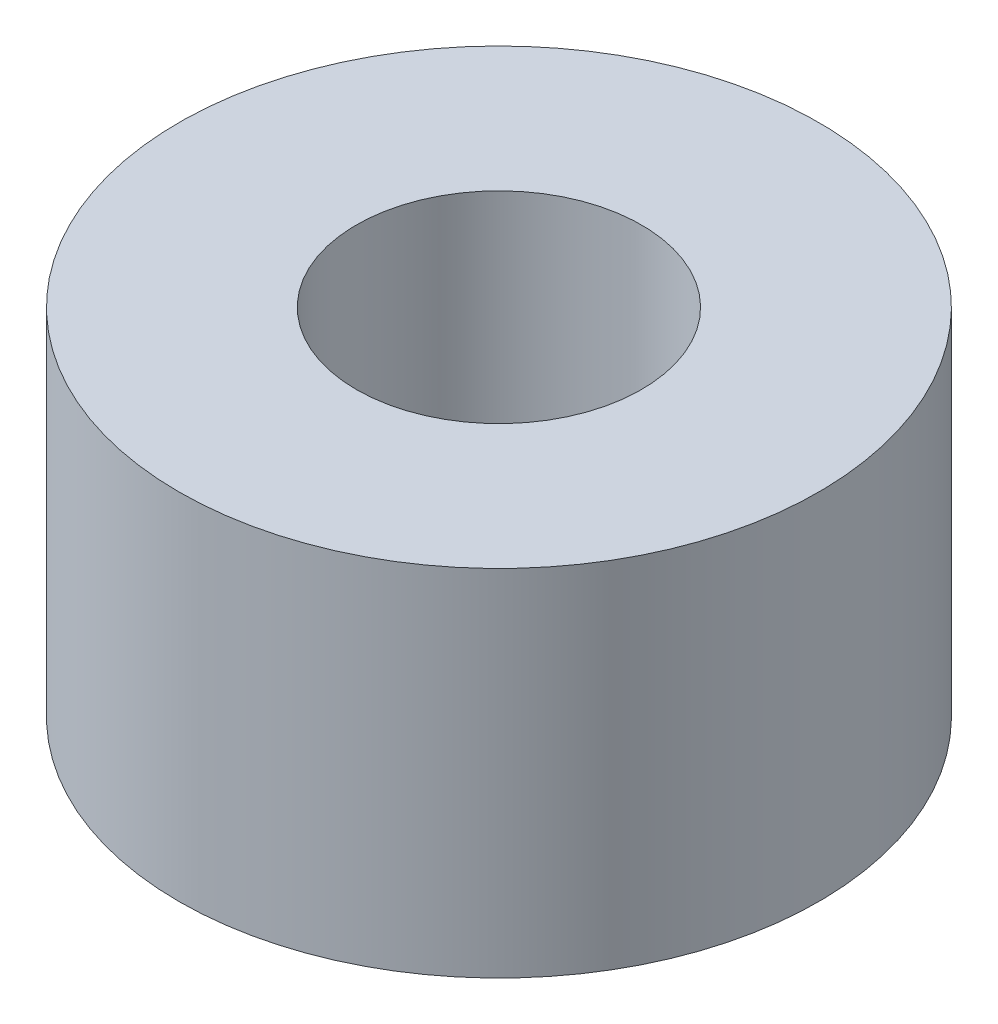
SolidWorks part; units mm, degrees
material "PET"
ref_plane "Front" through (0, 0, 0) normal (0, 0, 1) x (1, 0, 0)
ref_plane "Top" through (0, 0, 0) normal (0, 1, 0) x (1, 0, 0)
ref_plane "Right" through (0, 0, 0) normal (1, 0, 0) x (0, 0, -1)
sketch "Sketch1" plane through (0, 0, 0) normal (0, 1, 0) x (1, 0, 0)
  circle A0 centre (0, 0) radius 2.5527
  circle A1 centre (0, 0) radius 5.7277
  dimension "D1" = 3.175
  dimension "D2" = 5.1054
extrude "Boss-Extrude1" add sketch "Sketch1" along normal blind 6.35
